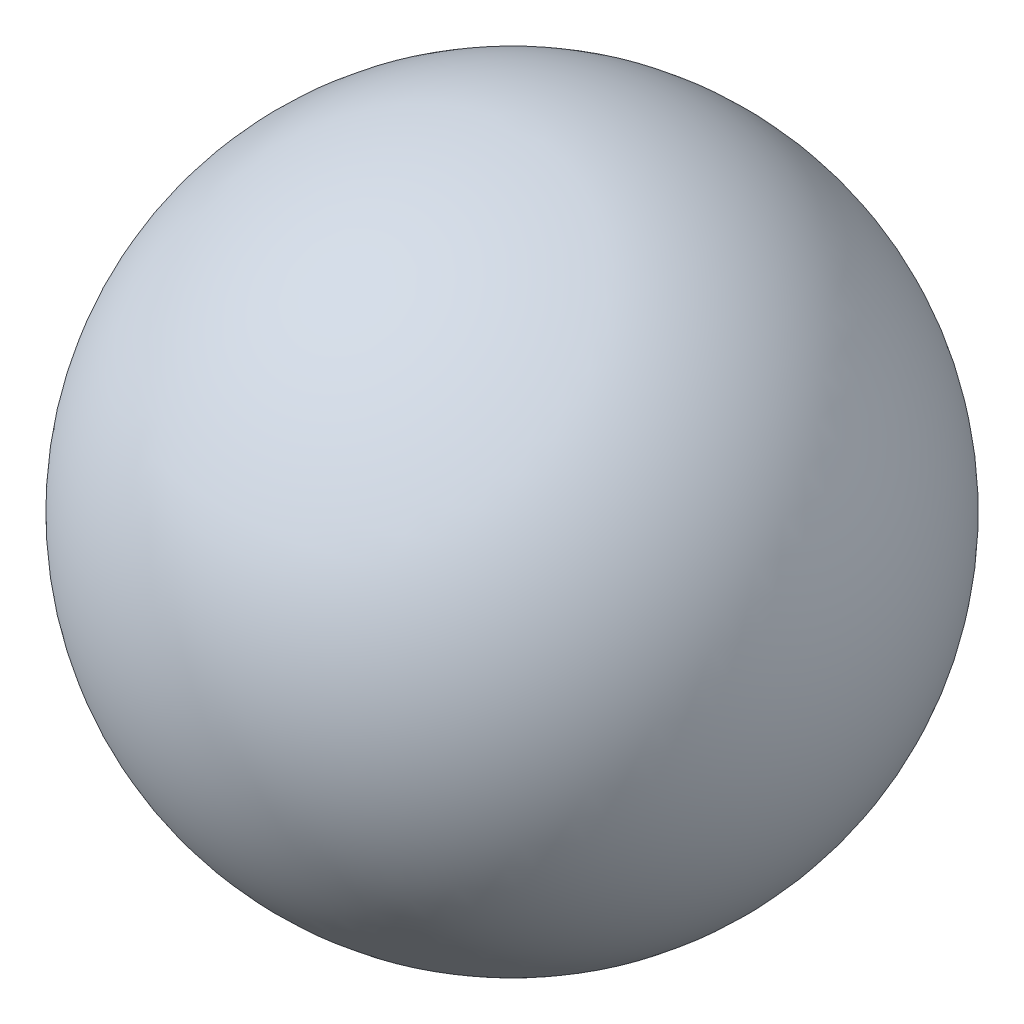
SolidWorks part; units mm, degrees
ref_plane "Front Plane" through (0, 0, 0) normal (0, 0, 1) x (1, 0, 0)
ref_plane "Top Plane" through (0, 0, 0) normal (0, 1, 0) x (1, 0, 0)
ref_plane "Right Plane" through (0, 0, 0) normal (1, 0, 0) x (0, 0, -1)
sketch "Sketch1" plane through (0, 0, 0) normal (0, 0, 1) x (1, 0, 0)
  line L0 (0, 304.8) -> (0, -304.8) construction
  line L1 (0, 304.8) -> (0, -304.8)
  arc A0 (0, -304.8) -> (0, 304.8) centre (0, 0) ccw
  dimension "D1" = 609.6
revolve "Revolve6" add sketch "Sketch1" angle 360 about L0
